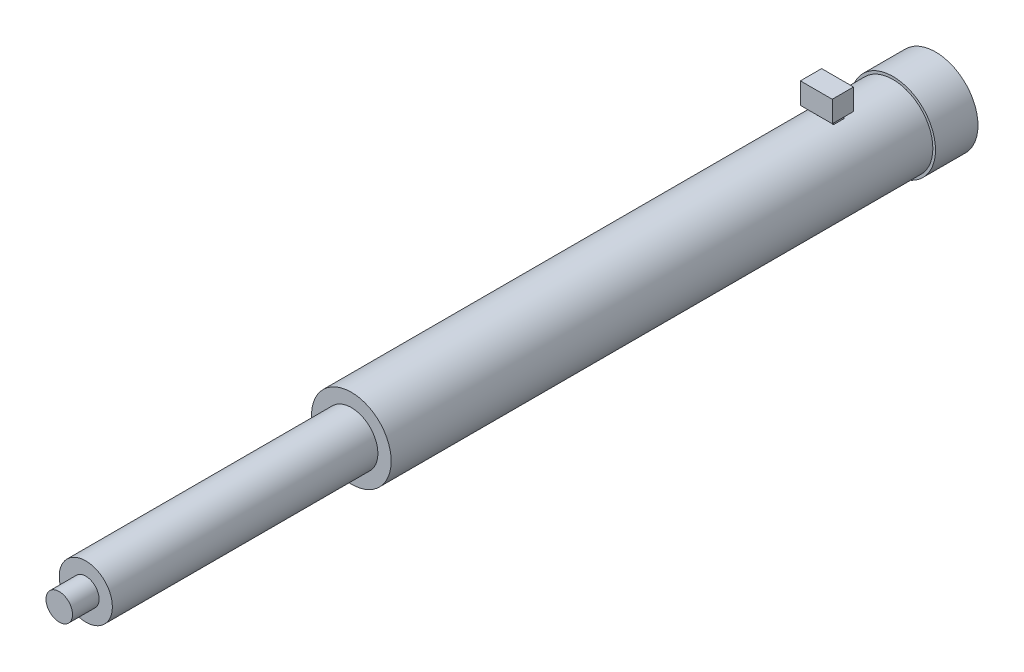
SolidWorks part; units mm, degrees
ref_plane "Front Plane" through (0, 0, 0) normal (0, 0, 1) x (1, 0, 0)
ref_plane "Top Plane" through (0, 0, 0) normal (0, 1, 0) x (1, 0, 0)
ref_plane "Right Plane" through (0, 0, 0) normal (1, 0, 0) x (0, 0, -1)
sketch "Sketch2" plane through (0, 0, 0) normal (0, 0, 1) x (1, 0, 0)
  circle A0 centre (0, 0) radius 10.16
  dimension "D1" = 20.32
extrude "Boss-Extrude1" add sketch "Sketch2" along normal blind 10.16
sketch "Sketch3" plane through (0, 0, 10.16) normal (0, 0, 1) x (1, 0, 0)
  circle A0 centre (0, 0) radius 9.525
  dimension "D1" = 19.05
extrude "Boss-Extrude2" add sketch "Sketch3" along normal blind 129.54
sketch "Sketch4" plane through (0, 0, 139.7) normal (0, 0, 1) x (1, 0, 0)
  circle A0 centre (0, 0) radius 6.35
  dimension "D1" = 12.7
extrude "Boss-Extrude4" add sketch "Sketch4" along normal blind 63.5
sketch "Sketch5" plane through (0, 0, 203.2) normal (0, 0, 1) x (1, 0, 0)
  circle A0 centre (0, 0) radius 3.175
  dimension "D1" = 6.35
extrude "Boss-Extrude5" add sketch "Sketch5" along normal blind 6.35
ref_plane "Plane2" through (0, 2.54, 0) normal (0, 1, 0) x (1, 0, 0)
sketch "Sketch8" plane through (0, 2.54, 0) normal (0, 1, 0) x (1, 0, 0)
  line L0 (-2.032, -23.9154) -> (-0.762, -23.9154)
  line L1 (0.762, -23.9154) -> (2.032, -23.9154)
  line L2 (-2.032, -23.9154) -> (-0.762, -23.9154)
  line L3 (-2.032, -23.9154) -> (-2.032, -26.4554)
  line L4 (-2.032, -26.4554) -> (-0.762, -26.4554)
  line L5 (-0.762, -23.9154) -> (-0.762, -26.4554)
  line L6 (0.762, -26.5407) -> (2.032, -26.5407)
  line L7 (0.762, -26.5407) -> (0.762, -23.9154)
  line L8 (0.762, -23.9154) -> (2.032, -23.9154)
  line L9 (2.032, -26.5407) -> (2.032, -23.9154)
  point P3 (0, -23.9154)
  dimension "D1" = 1.27
  dimension "D2" = 1.27
  dimension "D3" = 2.54
  dimension "D4" = 2.6253
  dimension "D5" = 0.762
  dimension "D6" = 0.762
extrude "Extrude-Thin1" add sketch "Sketch8" along normal blind 8.89 thin contours L1 | L0
sketch "Sketch9" plane through (0, 11.43, 0) normal (0, 1, 0) x (1, 0, 0)
  line L1 (3.81, -23.4245) -> (-3.81, -23.4245)
  line L2 (3.81, -23.4245) -> (3.81, -28.5045)
  line L3 (3.81, -28.5045) -> (-3.81, -28.5045)
  line L4 (-3.81, -23.4245) -> (-3.81, -28.5045)
  point P4 (0, -23.4245)
  dimension "D1" = 7.62
  dimension "D2" = 5.08
extrude "Boss-Extrude14" add sketch "Sketch9" along normal blind 5.08
